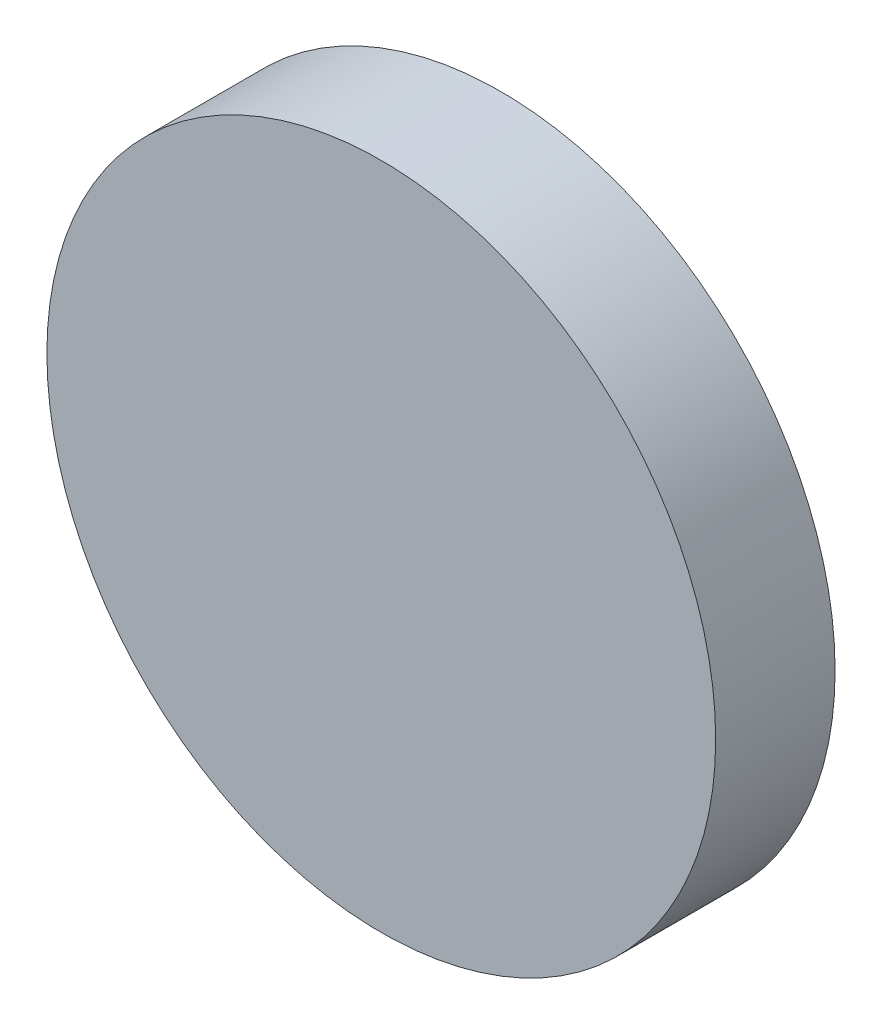
SolidWorks part; units mm, degrees
ref_plane "Front Plane" through (0, 0, 0) normal (0, 0, 1) x (1, 0, 0)
ref_plane "Top Plane" through (0, 0, 0) normal (0, 1, 0) x (1, 0, 0)
ref_plane "Right Plane" through (0, 0, 0) normal (1, 0, 0) x (0, 0, -1)
sketch "Sketch1" plane through (0, 0, 0) normal (0, 1, 0) x (1, 0, 0)
  line L0 (0, 48.7102) -> (0, -49.5867)
  line L1 (0, 48.7102) -> (14, 48.7102)
  line L2 (14, 48.7102) -> (14, 43.7102)
  line L3 (14, 43.7102) -> (-0.1643, 43.7102)
  line L4 (14, 48.7102) -> (12, 48.7102)
  line L5 (12, 48.7102) -> (12, 48.2102)
  line L6 (12, 48.2102) -> (10, 48.2102)
  line L8 (0, -2.75) -> (0, 2.75) construction
  arc A0 (10, 48.2102) -> (0, 44.0082) centre (0, 58.0082) cw
  dimension "D1" = 2
  dimension "D6" = 14
  dimension "D2" = 0.5
  dimension "D3" = 5
  dimension "D4" = 14.1643
  dimension "D5" = 14
  dimension "D7" = 0
  dimension "D8" = 0
  dimension "D9" = 0
revolve "Revolve1" add sketch "Sketch1" angle 360 about L0
sketch "Sketch2" plane through (0, 0, -48.7102) normal (0, 0, -1) x (-1, 0, 0)
  line L0 (-1.25, 13.6) -> (1.25, 13.6)
  line L1 (-13.6, -1.25) -> (-12.4, -1.25)
  line L2 (-13.6, -1.25) -> (-13.6, 1.25)
  line L3 (-13.6, 1.25) -> (-12.4, 1.25)
  line L4 (-12.4, -1.25) -> (-12.4, 1.25)
  line L5 (-13.6, -1.25) -> (-12.4, 1.25) construction
  line L6 (-13.6, 1.25) -> (-12.4, -1.25) construction
  line L7 (7.7903, 0) -> (-7.7903, 0) construction
  line L8 (0, 2.75) -> (0, -2.75) construction
  line L9 (-1.25, 13.6) -> (-1.25, 12.4)
  line L10 (-1.25, 12.4) -> (1.25, 12.4)
  line L11 (1.25, 13.6) -> (1.25, 12.4)
  line L12 (13.6, 1.25) -> (13.6, -1.25)
  line L13 (13.6, 1.25) -> (12.4, 1.25)
  line L14 (12.4, 1.25) -> (12.4, -1.25)
  line L15 (13.6, -1.25) -> (12.4, -1.25)
  line L16 (1.25, -13.6) -> (-1.25, -13.6)
  line L17 (1.25, -13.6) -> (1.25, -12.4)
  line L18 (1.25, -12.4) -> (-1.25, -12.4)
  line L19 (-1.25, -13.6) -> (-1.25, -12.4)
  point P0 (-13, 0)
  point P24 (0, 0)
  dimension "D5" = 4
  dimension "D1" = 2.5
  dimension "D2" = 1.2
  dimension "D3" = 1.25
  dimension "D4" = 12.4
extrude "Cut-Extrude1" cut sketch "Sketch2" against normal blind 4
